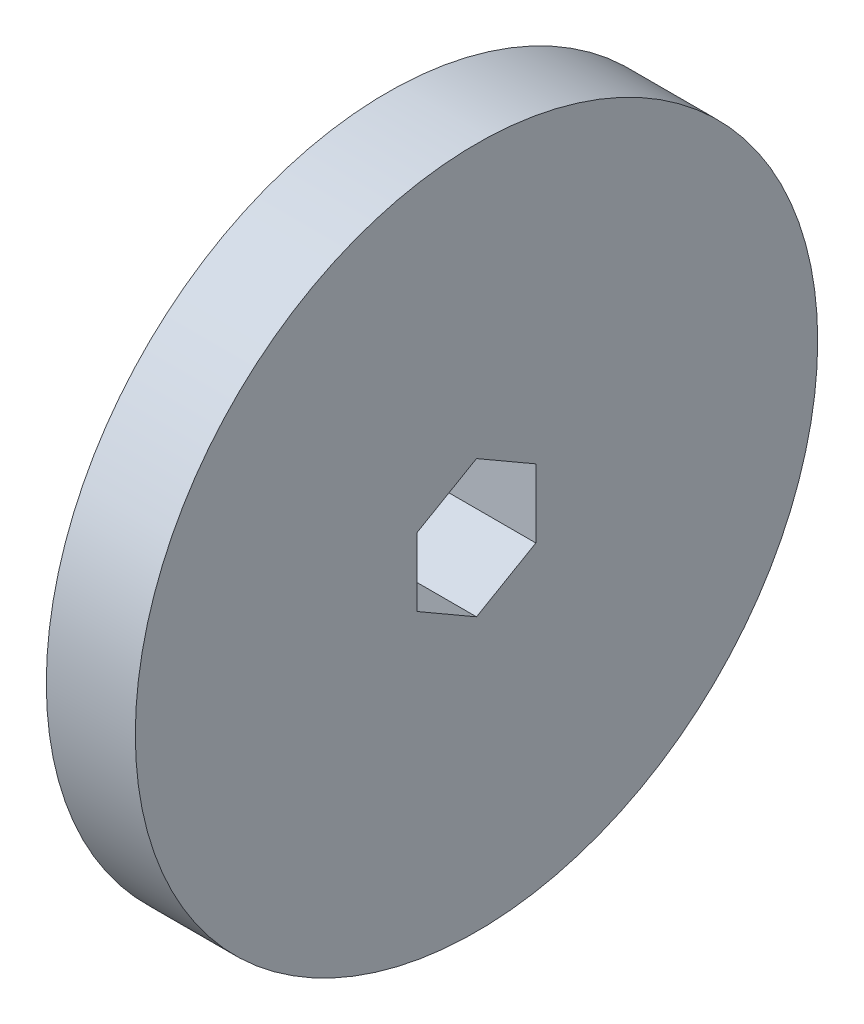
SolidWorks part; units mm, degrees
ref_plane "Front Plane" through (0, 0, 0) normal (0, 0, 1) x (1, 0, 0)
ref_plane "Top Plane" through (0, 0, 0) normal (0, 1, 0) x (1, 0, 0)
ref_plane "Right Plane" through (0, 0, 0) normal (1, 0, 0) x (0, 0, -1)
sketch "Sketch2" plane through (0, 0, 0) normal (1, 0, 0) x (0, 0, -1)
  line L1 (0, 7.3323) -> (-6.35, 3.6662)
  line L2 (-6.35, 3.6662) -> (-6.35, -3.6662)
  line L3 (-6.35, -3.6662) -> (0, -7.3323)
  line L4 (0, -7.3323) -> (6.35, -3.6662)
  line L5 (6.35, -3.6662) -> (6.35, 3.6662)
  line L6 (6.35, 3.6662) -> (0, 7.3323)
  circle A0 centre (0, 0) radius 36.5125
  circle A1 centre (0, 0) radius 6.35 construction
  dimension "D1" = 73.025
  dimension "D2" = 12.7
extrude "Boss-Extrude1" add sketch "Sketch2" along normal mid plane 9.525
